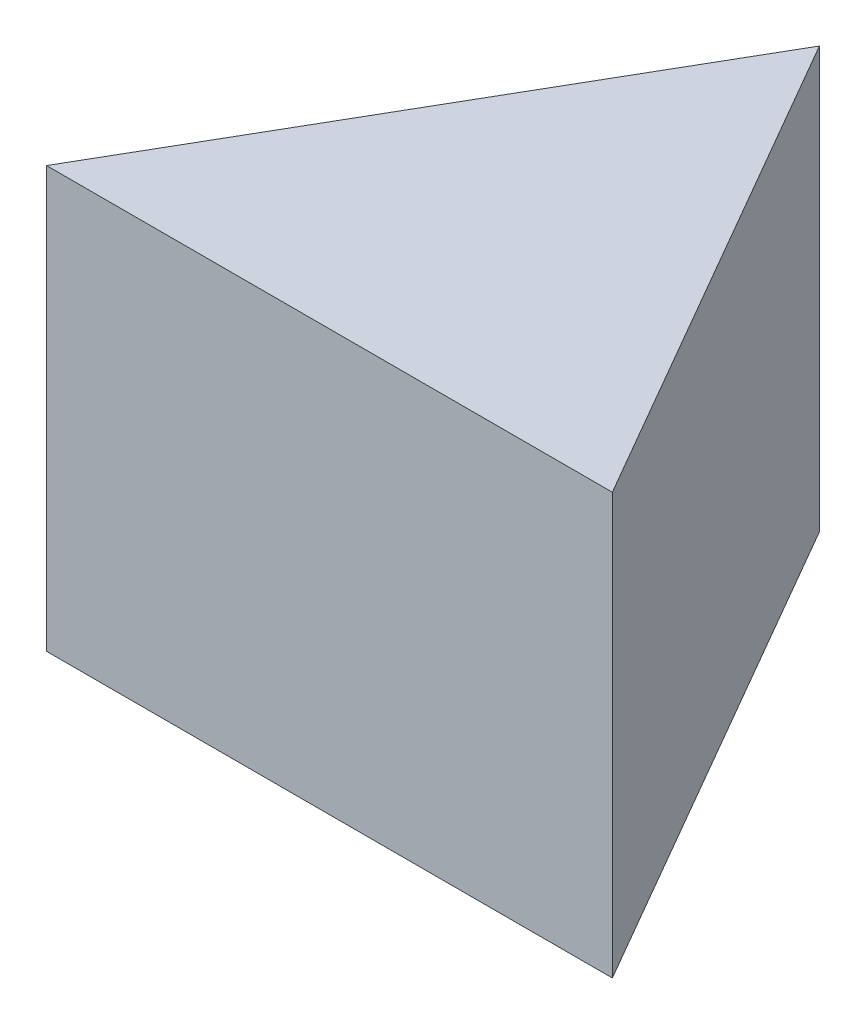
SolidWorks part; units mm, degrees
material "鎳"
ref_plane "前基準面" through (0, 0, 0) normal (0, 0, 1) x (1, 0, 0)
ref_plane "上基準面" through (0, 0, 0) normal (0, 1, 0) x (1, 0, 0)
ref_plane "右基準面" through (0, 0, 0) normal (1, 0, 0) x (0, 0, -1)
sketch "草圖1" plane through (0, 0, 0) normal (0, 1, 0) x (1, 0, 0)
  line L0 (0, 0) -> (39, 0)
  line L1 (39, 0) -> (19.5, 33.775)
  line L2 (19.5, 33.775) -> (0, 0)
  dimension "D1" = 39
extrude "填料-伸長1" add sketch "草圖1" along normal blind 29
sketch3d "URDF Reference"
  line L0 (0, 0, 0) -> (10, 0, 0) construction
  line L1 (0, 0, 0) -> (0, 0, -10) construction
  point P0 (0, 0, 0)
  point P1 (0, 0, 0)
